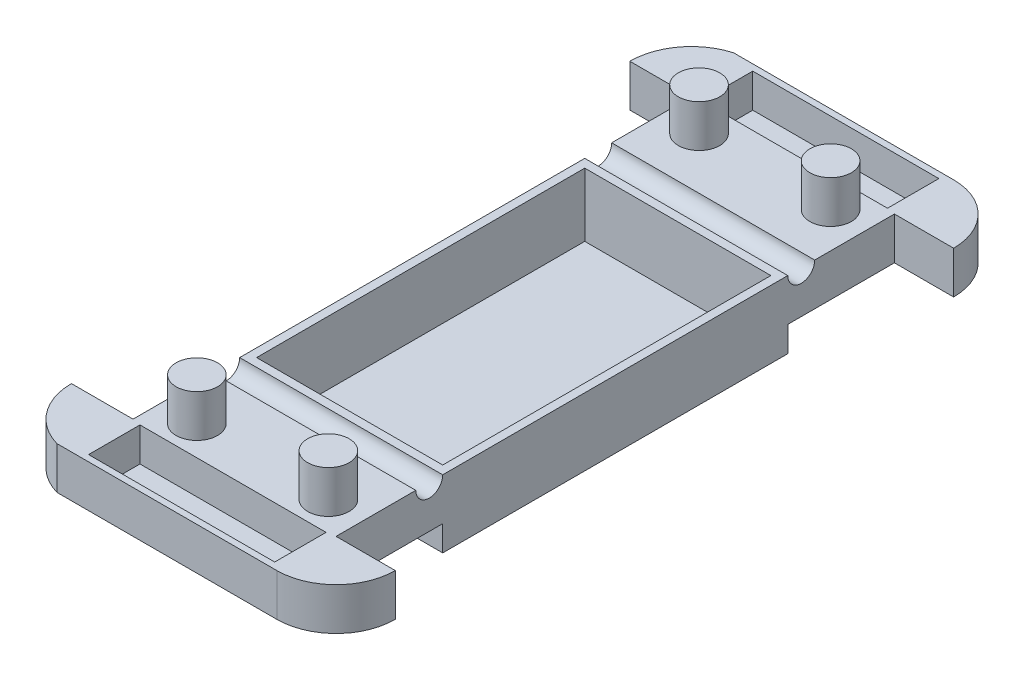
SolidWorks part; units mm, degrees
ref_plane "Front Plane" through (0, 0, 0) normal (0, 0, 1) x (1, 0, 0)
ref_plane "Top Plane" through (0, 0, 0) normal (0, 1, 0) x (1, 0, 0)
ref_plane "Right Plane" through (0, 0, 0) normal (1, 0, 0) x (0, 0, -1)
sketch "Sketch1" plane through (0, 0, 0) normal (0, 1, 0) x (1, 0, 0)
  line L1 (-24.8944, 17.78) -> (41.1456, 17.78)
  line L2 (-19.8144, 0) -> (-19.8144, -167.64)
  line L3 (-24.8944, -185.42) -> (41.1456, -185.42)
  line L4 (41.1456, 0) -> (41.1456, -167.64)
  line L5 (58.9256, 0) -> (41.1456, 0)
  line L6 (-38.3059, -167.64) -> (-19.8144, -167.64)
  line L7 (-38.3059, 0) -> (-19.8144, 0)
  line L8 (58.9256, -167.64) -> (41.1456, -167.64)
  arc A0 (58.9256, 0) -> (41.1456, 17.78) centre (41.1456, 0) ccw
  arc A1 (-38.3059, 0) -> (-24.8944, 17.78) centre (-19.8144, 0) cw
  arc A2 (-38.3059, -167.64) -> (-24.8944, -185.42) centre (-19.8144, -167.64) ccw
  arc A3 (58.9256, -167.64) -> (41.1456, -185.42) centre (41.1456, -167.64) cw
  dimension "D1" = 66.04
  dimension "D2" = 203.2
  dimension "D3" = 60.96
  dimension "0.8" = 17.78
extrude "Boss-Extrude1" add sketch "Sketch1" along normal blind 12.7 contours L1 A0 L5 L4 L8 A3 L3 A2 L6 L2 L7 A1
sketch "Sketch3" plane through (41.1456, 0, 0) normal (1, 0, 0) x (0, 0, -1)
  line L0 (0, 12.7) -> (-167.64, 12.7) construction
  circle A0 centre (-139.6638, 12.7) radius 4.0396
  circle A1 centre (-27.9739, 12.7) radius 4.0396
extrude "Cut-Extrude1" cut sketch "Sketch3" against normal through all
sketch "Sketch4" plane through (0, 12.7, 0) normal (0, 1, 0) x (1, 0, 0)
  line L0 (10.6656, 17.78) -> (10.6656, -185.42)
  line L5 (-24.8944, 17.78) -> (41.1456, 17.78) construction
  line L6 (-24.8944, -185.42) -> (41.1456, -185.42) construction
  line L7 (41.1456, -32.0134) -> (41.1456, -135.6242) construction
  circle A0 centre (30.4166, -8.428) radius 6.2278
  circle A2 centre (30.4166, -159.212) radius 6.2278
  circle A4 centre (-9.0854, -159.212) radius 6.2278
  circle A5 centre (-9.0854, -8.428) radius 6.2278
  dimension "D1" = 30.48
extrude "Boss-Extrude3" add sketch "Sketch4" along normal blind 12.7 contours A5 | A0 | A4 | A2
sketch "Sketch5" plane through (0, 12.7, 0) normal (0, 1, 0) x (1, 0, 0)
  line L1 (-17.2744, -34.5534) -> (38.6056, -34.5534)
  line L2 (-17.2744, -34.5534) -> (-17.2744, -133.0842)
  line L3 (-17.2744, -133.0842) -> (38.6056, -133.0842)
  line L4 (38.6056, -34.5534) -> (38.6056, -133.0842)
  line L9 (41.1456, -32.0134) -> (41.1456, -135.6242) construction
  line L10 (-19.8144, -32.0134) -> (-19.8144, -135.6242) construction
  line L11 (41.1456, -32.0134) -> (-19.8144, -32.0134) construction
  line L12 (-19.8144, -135.6242) -> (41.1456, -135.6242) construction
  dimension "D1" = 2.54
  dimension "0.1" = 2.54
  dimension "D2" = 2.54
  dimension "D3" = 2.54
extrude "Cut-Extrude2" cut sketch "Sketch5" against normal through all and the other way through all
sketch "Sketch6" plane through (0, 12.7, 0) normal (0, 1, 0) x (1, 0, 0)
  line L0 (-19.8144, 0) -> (-19.8144, -23.9343) construction
  line L1 (-17.2744, 15.8868) -> (38.6056, 15.8868)
  line L2 (-17.2744, 15.8868) -> (-17.2744, 0.462)
  line L3 (-17.2744, 0.462) -> (38.6056, 0.462)
  line L4 (38.6056, 15.8868) -> (38.6056, 0.462)
  line L5 (41.1456, 0) -> (41.1456, -23.9343) construction
  line L6 (-19.8144, -83.82) -> (41.1456, -83.82)
  line L7 (-19.8144, -32.0134) -> (-19.8144, -135.6242) construction
  line L8 (41.1456, -32.0134) -> (41.1456, -135.6242) construction
  line L9 (-24.8944, -185.42) -> (41.1456, -185.42) construction
  line L10 (-17.2744, -168.102) -> (38.6056, -168.102)
  line L11 (38.6056, -183.5268) -> (38.6056, -168.102)
  line L12 (-17.2744, -183.5268) -> (38.6056, -183.5268)
  line L13 (-17.2744, -183.5268) -> (-17.2744, -168.102)
  circle A0 centre (-9.0854, -8.428) radius 6.2278 construction
  dimension "D1" = 8.89
  dimension "D2" = 2.54
  dimension "D3" = 2.54
  dimension "D4" = 101.6
extrude "Cut-Extrude3" cut sketch "Sketch6" against normal blind 10.16 contours L13 L12 L11 L10 | L4 L1 L2 L3
sketch "Sketch7" plane through (0, 0, 0) normal (0, -1, 0) x (1, 0, 0)
  line L1 (41.1456, 135.6242) -> (-19.8144, 135.6242)
  line L2 (41.1456, 135.6242) -> (41.1456, 32.0134)
  line L3 (41.1456, 32.0134) -> (-19.8144, 32.0134)
  line L4 (-19.8144, 135.6242) -> (-19.8144, 32.0134)
extrude "Boss-Extrude4" add sketch "Sketch7" along normal blind 7.62
sketch "Sketch8" plane through (0, 0, 0) normal (0, 1, 0) x (1, 0, 0)
  line L1 (-17.2744, -34.5534) -> (38.6056, -34.5534)
  line L2 (-17.2744, -34.5534) -> (-17.2744, -133.0842)
  line L3 (-17.2744, -133.0842) -> (38.6056, -133.0842)
  line L4 (38.6056, -34.5534) -> (38.6056, -133.0842)
extrude "Cut-Extrude4" cut sketch "Sketch8" against normal mid plane 12.7
